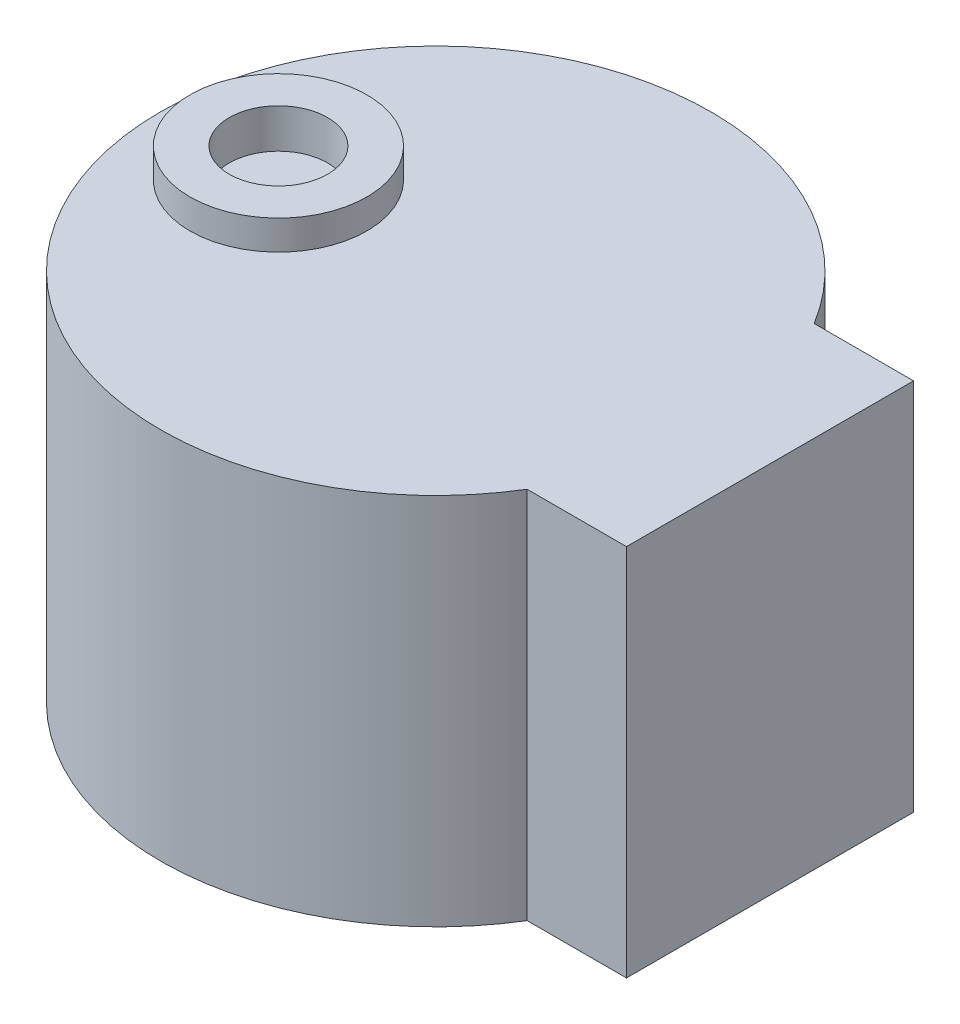
SolidWorks part; units mm, degrees
ref_plane "Alzado" through (0, 0, 0) normal (0, 0, 1) x (1, 0, 0)
ref_plane "Planta" through (0, 0, 0) normal (0, 1, 0) x (1, 0, 0)
ref_plane "Vista lateral" through (0, 0, 0) normal (1, 0, 0) x (0, 0, -1)
sketch "Croquis1" plane through (0, 0, 0) normal (0, 1, 0) x (1, 0, 0)
  line L0 (0, 0) -> (14, 0)
  line L2 (2.8442, -7.3) -> (17, -7.3)
  line L3 (2.8442, -7.3) -> (2.8442, 7.3)
  line L4 (2.8442, 7.3) -> (17, 7.3)
  line L5 (17, -7.3) -> (17, 7.3)
  line L6 (2.8442, -7.3) -> (17, 7.3) construction
  line L7 (2.8442, 7.3) -> (17, -7.3) construction
  circle A0 centre (0, 0) radius 14
  point P3 (9.9221, 0)
  dimension "D1" = 28
  dimension "D2" = 17
  dimension "D3" = 14.6
extrude "Saliente-Extruir1" add sketch "Croquis1" along normal blind 19
sketch "Croquis2" plane through (0, 19, 0) normal (0, 1, 0) x (1, 0, 0)
  circle A0 centre (-8, 0) radius 4.5
  dimension "D1" = 9
extrude "Saliente-Extruir2" add sketch "Croquis2" along normal blind 1.5
sketch "Croquis3" plane through (0, 20.5, 0) normal (0, 1, 0) x (1, 0, 0)
  circle A0 centre (-8, 0) radius 2.5
  dimension "D1" = 5
extrude "Saliente-Extruir3" add sketch "Croquis3" along normal blind 2.5
sketch "Croquis4" plane through (0, 23, 0) normal (0, 1, 0) x (1, 0, 0)
  line L1 (-9.5, -3.4931) -> (-6.5, -3.4931)
  line L2 (-9.5, -3.4931) -> (-9.5, 3.4931)
  line L3 (-9.5, 3.4931) -> (-6.5, 3.4931)
  line L4 (-6.5, -3.4931) -> (-6.5, 3.4931)
  line L5 (-9.5, -3.4931) -> (-6.5, 3.4931) construction
  line L6 (-9.5, 3.4931) -> (-6.5, -3.4931) construction
  circle A0 centre (-8, 0) radius 2.5
  circle M2 centre (-8, 0) radius 2.5
  dimension "D1" = 3
extrude "Saliente-Extruir4" add sketch "Croquis4" along normal blind 6 contours L4 L2 M2
sketch "Croquis5" plane through (0, 20.5, 0) normal (0, 1, 0) x (1, 0, 0)
  circle A0 centre (-8, 0) radius 2.5
extrude "Cortar-Extruir1" cut sketch "Croquis5" against normal blind 2 and the other way blind 10
